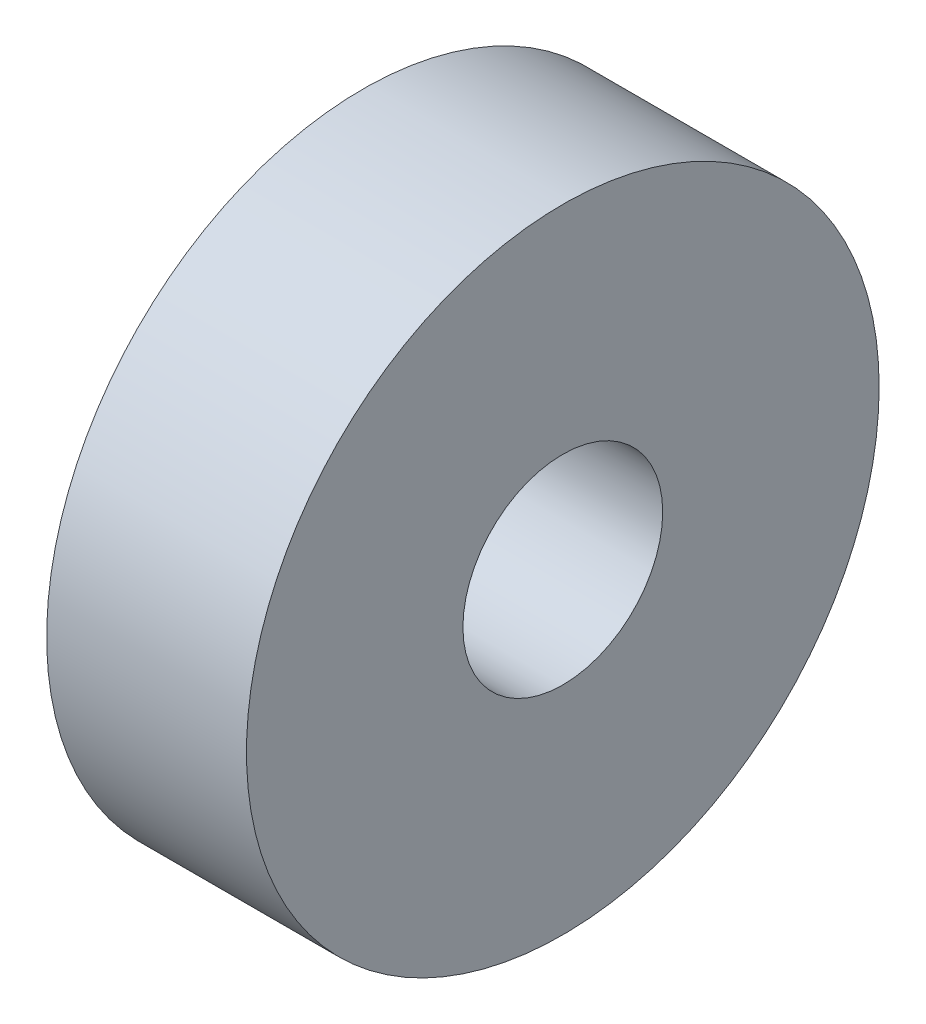
SolidWorks part; units mm, degrees
material "Chrome Stainless Steel"
ref_plane "Front Plane" through (0, 0, 0) normal (0, 0, 1) x (1, 0, 0)
ref_plane "Top Plane" through (0, 0, 0) normal (0, 1, 0) x (1, 0, 0)
ref_plane "Right Plane" through (0, 0, 0) normal (1, 0, 0) x (0, 0, -1)
sketch "Sketch1" plane through (0, 0, 0) normal (1, 0, 0) x (0, 0, -1)
  circle A0 centre (0, 0) radius 3
  circle A1 centre (0, 0) radius 9.5
  dimension "D1" = 6
  dimension "D2" = 19
extrude "Boss-Extrude1" add sketch "Sketch1" along normal blind 6
